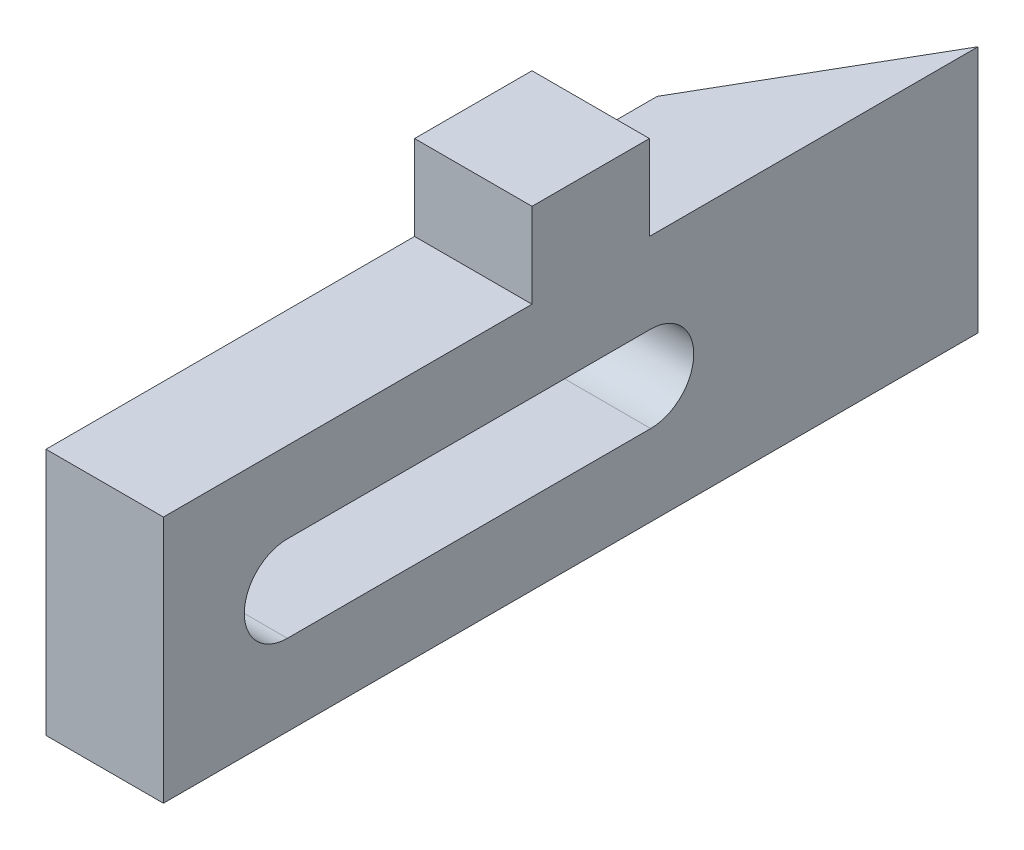
SolidWorks part; units mm, degrees
ref_plane "Front Plane" through (0, 0, 0) normal (0, 0, 1) x (1, 0, 0)
ref_plane "Top Plane" through (0, 0, 0) normal (0, 1, 0) x (1, 0, 0)
ref_plane "Right Plane" through (0, 0, 0) normal (1, 0, 0) x (0, 0, -1)
sketch "Sketch1" plane through (0, 0, 0) normal (0, 1, 0) x (1, 0, 0)
  line L0 (0, 0) -> (75, 0) construction
  line L1 (75, 0) -> (37.5, 64.9519) construction
  line L2 (37.5, 64.9519) -> (0, 0) construction
  line L3 (37.5, 64.9519) -> (37.5, 0) construction
  line L4 (15.5, 26.8468) -> (15.5, -20)
  line L5 (15.5, -20) -> (24.5, -20)
  line L6 (24.5, -20) -> (24.5, 42.4352)
  line L7 (24.5, 42.4352) -> (15.5, 26.8468)
  dimension "D1" = 75
  dimension "D2" = 75
  dimension "D3" = 75
  dimension "D4" = 13
  dimension "D5" = 9
  dimension "D6" = 20
extrude "Boss-Extrude1" add sketch "Sketch1" along normal blind 19
sketch "Sketch3" plane through (15.5, 0, 0) normal (-1, 0, 0) x (0, 0, 1)
  line L0 (-17.3468, 9.5) -> (10.5, 9.5) construction
  line L1 (-17.3468, 12.8) -> (10.5, 12.8)
  line L2 (-17.3468, 6.2) -> (10.5, 6.2)
  line L3 (-26.8468, 19) -> (20, 19) construction
  line L4 (-26.8468, 19) -> (-26.8468, 0) construction
  line L5 (20, 19) -> (20, 0) construction
  arc A0 (-17.3468, 12.8) -> (-17.3468, 6.2) centre (-17.3468, 9.5) ccw
  arc A1 (10.5, 6.2) -> (10.5, 12.8) centre (10.5, 9.5) ccw
  point P2 (-3.4234, 9.5)
  dimension "D4" = 3.3
  dimension "D1" = 9.5
  dimension "D2" = 9.5
  dimension "D3" = 9.5
extrude "Cut-Extrude1" cut sketch "Sketch3" against normal through all
sketch "Sketch4" plane through (0, 19, 0) normal (0, 1, 0) x (1, 0, 0)
  line L0 (15.5, 8.25) -> (24.5, 8.25)
  line L1 (15.5, 26.8468) -> (15.5, -20) construction
  line L2 (24.5, -20) -> (24.5, 42.4352) construction
  line L3 (24.5, 8.25) -> (24.5, 17.25)
  line L4 (24.5, 17.25) -> (15.5, 17.25)
  line L5 (15.5, 17.25) -> (15.5, 8.25)
  line L6 (15.5, -20) -> (24.5, -20) construction
  dimension "D1" = 9
  dimension "D2" = 28.25
extrude "Boss-Extrude3" add sketch "Sketch4" along normal blind 6.5
